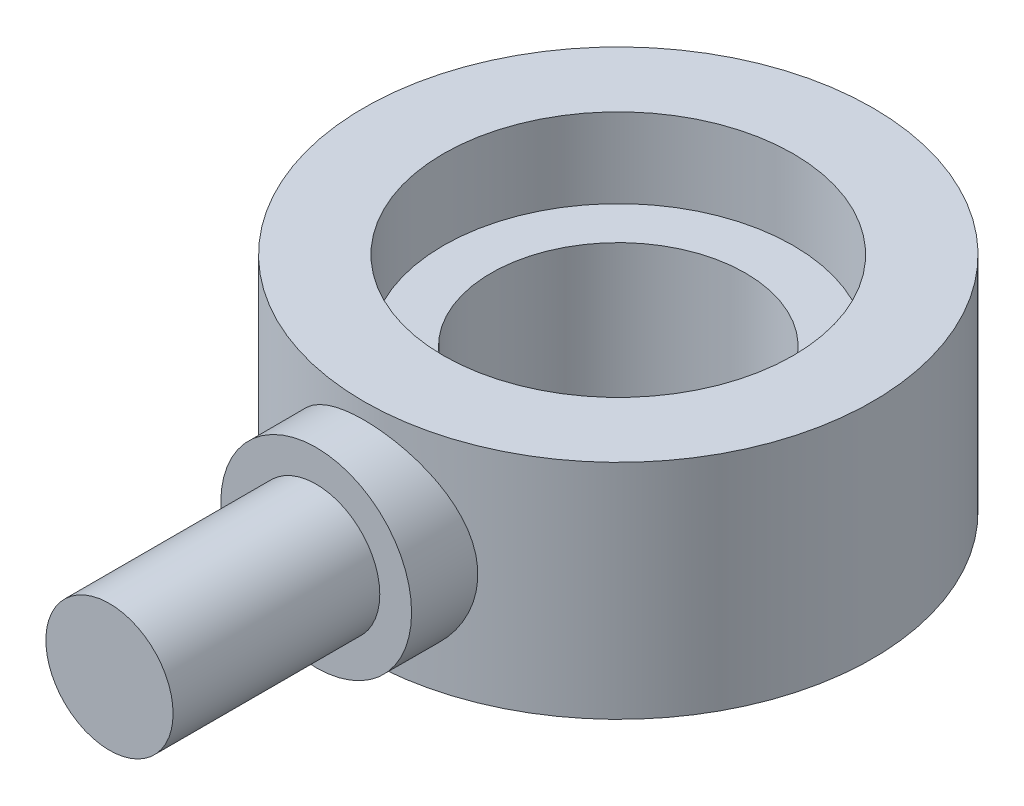
SolidWorks part; units mm, degrees
ref_plane "前视基准面" through (0, 0, 0) normal (0, 0, 1) x (1, 0, 0)
ref_plane "上视基准面" through (0, 0, 0) normal (0, 1, 0) x (1, 0, 0)
ref_plane "右视基准面" through (0, 0, 0) normal (1, 0, 0) x (0, 0, -1)
sketch "草图1" plane through (0, 0, 0) normal (0, 1, 0) x (1, 0, 0)
  circle A0 centre (0, 0) radius 8
  circle A1 centre (0, 0) radius 4
extrude "凸台-拉伸1" add sketch "草图1" along normal blind 7
sketch "草图2" plane through (0, 0, 0) normal (0, 0, 1) x (1, 0, 0)
  line L0 (-8, 3.5) -> (8, 3.5)
  line L1 (-8, 7) -> (-8, 0) construction
  line L2 (8, 0) -> (8, 7) construction
  line L3 (8, 3.5) -> (0, 0)
  line L4 (0, 0) -> (0, 7)
  line L5 (4, 7) -> (-4, 7) construction
  circle A0 centre (0, 3.5) radius 3
extrude "凸台-拉伸2" add sketch "草图2" along normal blind 9.5 contours A0
sketch "草图5" plane through (0, 7, 0) normal (0, 1, 0) x (1, 0, 0)
  circle A0 centre (0, 0) radius 4
extrude "切除-拉伸1" cut sketch "草图5" against normal blind 9.5
sketch "草图6" plane through (0, 0, 9.5) normal (0, 0, 1) x (1, 0, 0)
  circle A0 centre (0, 3.5) radius 2
extrude "凸台-拉伸3" add sketch "草图6" along normal blind 6.5
sketch "草图7" plane through (0, 7, 0) normal (0, 1, 0) x (1, 0, 0)
  circle A0 centre (0, 0) radius 5.5
extrude "切除-拉伸2" cut sketch "草图7" against normal blind 2.5
